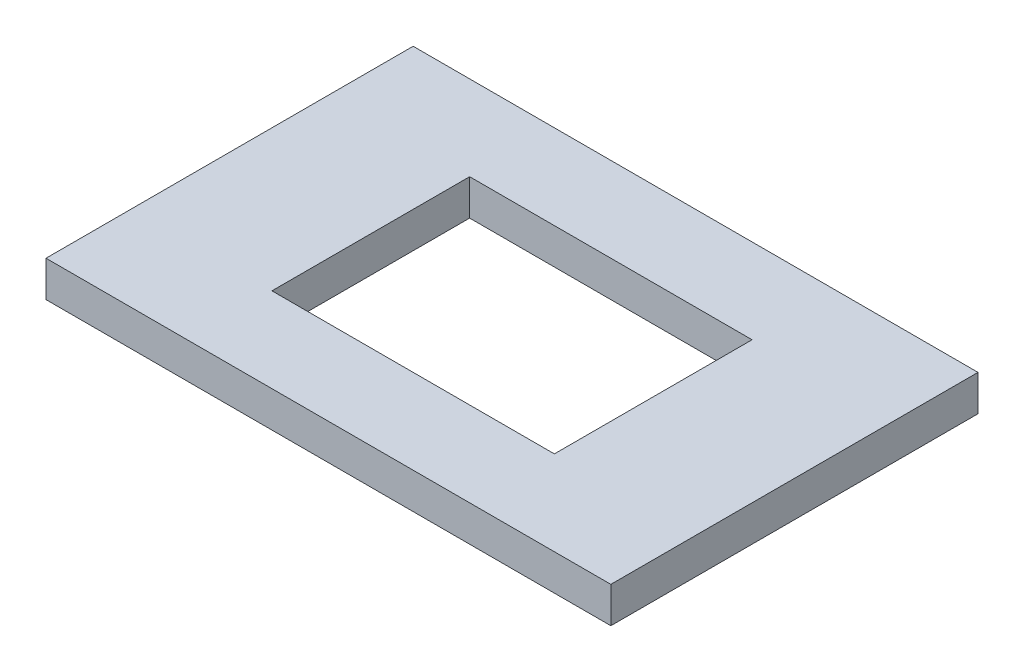
SolidWorks part; units mm, degrees
ref_plane "Front Plane" through (0, 0, 0) normal (0, 0, 1) x (1, 0, 0)
ref_plane "Top Plane" through (0, 0, 0) normal (0, 1, 0) x (1, 0, 0)
ref_plane "Right Plane" through (0, 0, 0) normal (1, 0, 0) x (0, 0, -1)
sketch "Sketch1" plane through (0, 0, 0) normal (0, 1, 0) x (1, 0, 0)
  line L1 (-58.08, 28.3897) -> (41.92, 28.3897)
  line L2 (-58.08, 28.3897) -> (-58.08, -36.6103)
  line L3 (-58.08, -36.6103) -> (41.92, -36.6103)
  line L4 (41.92, 28.3897) -> (41.92, -36.6103)
extrude "Boss-Extrude1" add sketch "Sketch1" along normal blind 6.35
sketch "Sketch2" plane through (0, 6.35, 0) normal (0, 1, 0) x (1, 0, 0)
  line L0 (-58.08, 28.3897) -> (-58.08, -36.6103) construction
  line L1 (-33.08, 13.3897) -> (16.92, 13.3897)
  line L2 (-33.08, 13.3897) -> (-33.08, -21.6103)
  line L3 (-33.08, -21.6103) -> (16.92, -21.6103)
  line L4 (16.92, 13.3897) -> (16.92, -21.6103)
  line L5 (41.92, -36.6103) -> (41.92, 28.3897) construction
  line L6 (41.92, 28.3897) -> (-58.08, 28.3897) construction
  line L7 (-58.08, -36.6103) -> (41.92, -36.6103) construction
  dimension "D1" = 25
  dimension "D2" = 25
  dimension "D3" = 15
  dimension "D4" = 15
extrude "Cut-Extrude1" cut sketch "Sketch2" against normal blind 6.35
